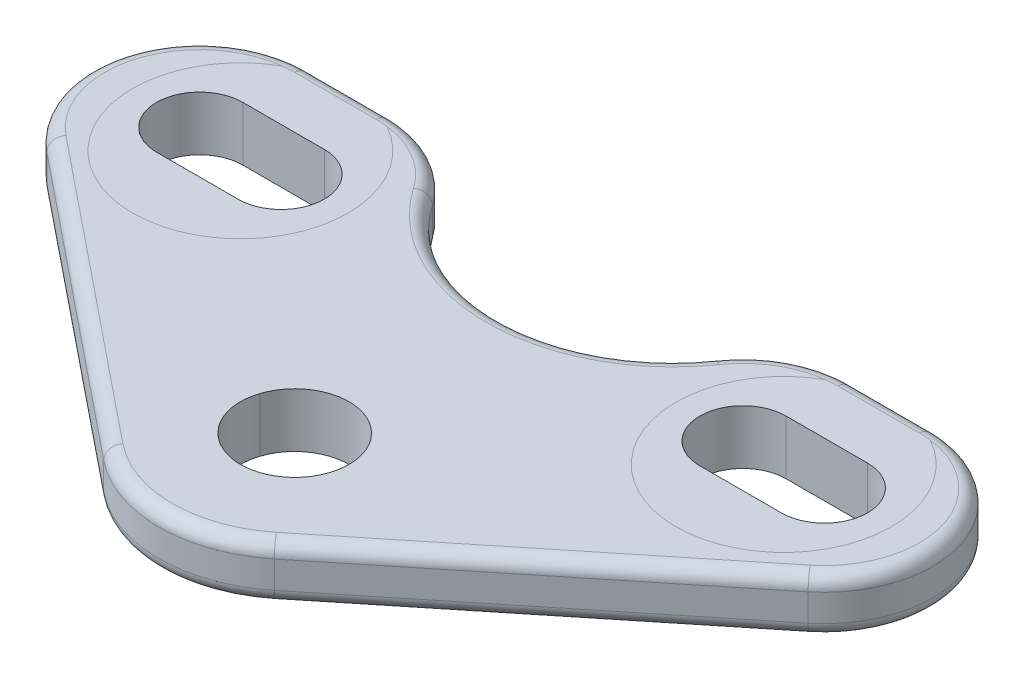
SolidWorks part; units mm, degrees
material "6061-T6 (SS)"
ref_plane "Front Plane" through (0, 0, 0) normal (0, 0, 1) x (1, 0, 0)
ref_plane "Top Plane" through (0, 0, 0) normal (0, 1, 0) x (1, 0, 0)
ref_plane "Right Plane" through (0, 0, 0) normal (1, 0, 0) x (0, 0, -1)
sketch "Sketch1" plane through (0, 0, 0) normal (0, 1, 0) x (1, 0, 0)
  line L0 (-23, 0) -> (-17, 0) construction
  line L1 (-23, 3.175) -> (-17, 3.175)
  line L2 (-23, -3.175) -> (-17, -3.175)
  line L3 (17, 0) -> (23, 0) construction
  line L4 (17, 3.175) -> (23, 3.175)
  line L5 (17, -3.175) -> (23, -3.175)
  line L6 (-28.0257, -6.2244) -> (-6.2821, -23.7805)
  line L7 (6.2821, -23.7805) -> (28.0257, -6.2244)
  line L8 (-23, 8) -> (-17, 8)
  line L9 (23, 8) -> (17, 8)
  arc A0 (-23, 3.175) -> (-23, -3.175) centre (-23, 0) ccw
  arc A1 (-17, -3.175) -> (-17, 3.175) centre (-17, 0) ccw
  arc A2 (17, 3.175) -> (17, -3.175) centre (17, 0) ccw
  arc A3 (23, -3.175) -> (23, 3.175) centre (23, 0) ccw
  arc A4 (-23, 8) -> (-28.0257, -6.2244) centre (-23, 0) ccw
  arc A5 (23, 8) -> (28.0257, -6.2244) centre (23, 0) cw
  circle A6 centre (0, -16) radius 4
  arc A7 (-6.2821, -23.7805) -> (6.2821, -23.7805) centre (0, -16) ccw
  arc A8 (-17, 8) -> (-10.43, 4.5645) centre (-17, 0) cw
  arc A9 (17, 8) -> (10.43, 4.5645) centre (17, 0) ccw
  arc A10 (-10.43, 4.5645) -> (10.43, 4.5645) centre (0, 11.8106) ccw
  point P2 (-20, 0)
  point P9 (20, 0)
  dimension "D4" = 6.35
  dimension "D5" = 8
  dimension "D7" = 8
  dimension "D9" = 10
  dimension "D1" = 12.7
  dimension "D2" = 20
  dimension "D3" = 6
  dimension "D6" = 16
extrude "Boss-Extrude1" add sketch "Sketch1" along normal blind 4
fillet "Fillet1" radius 1 20 edges at (-30.543, 0, -2.6651) (30.543, 0, -2.6651) (17.1539, 0, 15.0024) (0, 0, 26) (-30.543, 4, -2.6651) (30.543, 4, -2.6651) (17.1539, 4, 15.0024) (0, 4, 26) (-17.1539, 0, 15.0024) (-17.1539, 4, 15.0024) (-13.293, 0, -7.0893) (-20, 0, -8) (13.293, 0, -7.0893) (20, 0, -8) (-13.293, 4, -7.0893) (-20, 4, -8) (13.293, 4, -7.0893) (20, 4, -8) (0, 0, 0.8894) (0, 4, 0.8894)
sketch "Sketch2" plane through (0, 0, 0) normal (0, 1, 0) x (1, 0, 0)
  line L0 (-20, 3.175) -> (-20, -3.175) construction
  line L1 (-17, 3.175) -> (-23, 3.175) construction
  line L2 (-23, -3.175) -> (-17, -3.175) construction
  line L3 (20, 3.175) -> (20, -3.175) construction
  line L4 (23, 3.175) -> (17, 3.175) construction
  line L5 (17, -3.175) -> (23, -3.175) construction
  circle A0 centre (-20, 0) radius 7.94
  circle A1 centre (20, 0) radius 7.94
  dimension "D1" = 15.88
split line "Split Line1"
sketch "Sketch3" plane through (0, 0, 0) normal (0, 1, 0) x (1, 0, 0)
  line L0 (0, -16) -> (0, -29.9624) construction
  line L1 (0, -16) -> (-4.8214, -30.8386) construction
  line L2 (-7.4205, -13.5889) -> (7.4205, -18.4111)
  dimension "D1" = 18
split line "Split Line2"
sketch3d "3DSketch1"
  line L0 (0, 0, 16) -> (-4.8214, 2.7511, 30.8386) construction
  line L1 (0, 0, 16) -> (-4.8214, 0, 30.8386) construction
  dimension "D1" = 10
sketch3d "3DSketch2"
  line L0 (0, 4, 16) -> (0, 11.6, 16) construction
  line L2 (0, 0, 16) -> (0, -7.6, 16) construction
  arc A0 (3.8042, 4, 17.2361) -> (-3.8042, 4, 14.7639) centre (0, 4, 16) ccw construction
  point P9 (0, 8, 16)
  dimension "D1" = 7.6
